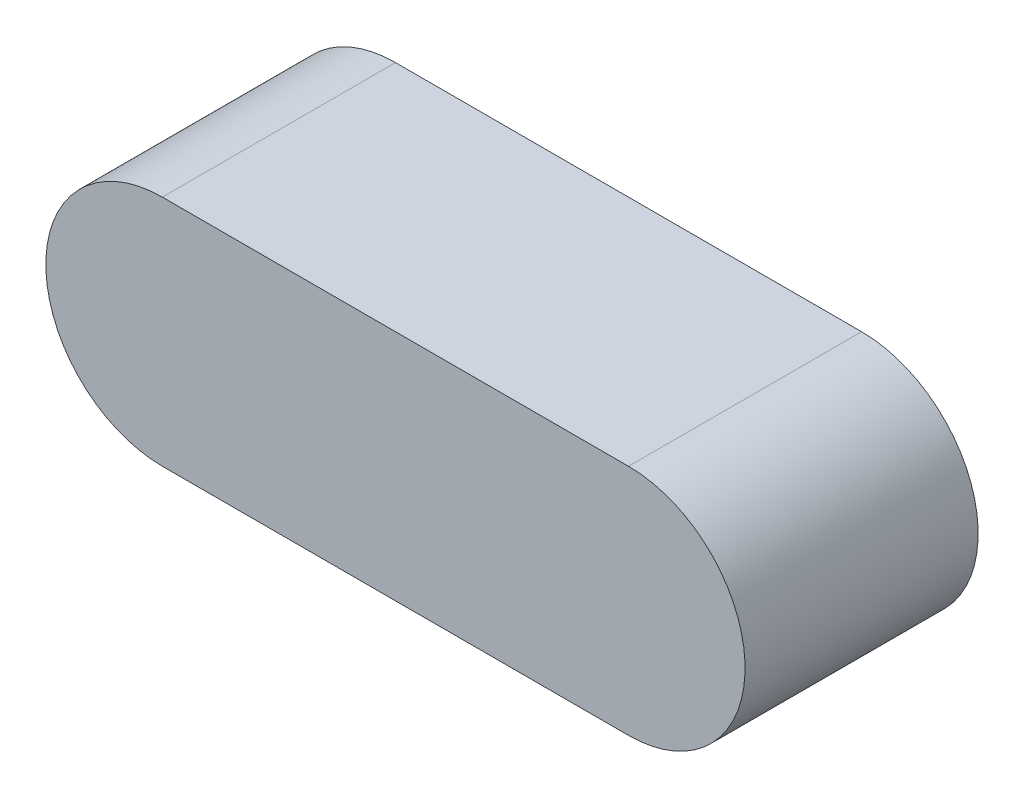
SolidWorks part; units mm, degrees
extrude "Base-Extrude" add sketch "Sketch1" along normal blind 3
sketch "Sketch1" plane through (0, 0, 0) normal (0, 0, 1) x (1, 0, 0)
  line L0 (-3, 1.5) -> (3, 1.5)
  line L1 (-3, -1.5) -> (3, -1.5)
  line L2 (-4.5, 0) -> (-4.5, 3.7182) construction
  line L3 (4.5, 0) -> (4.5, 3.2393) construction
  arc A0 (-3, 1.5) -> (-3, -1.5) centre (-3, 0) ccw
  arc A1 (3, -1.5) -> (3, 1.5) centre (3, 0) ccw
  dimension "D2" = 1.5
  dimension "D3" = 1.5
  dimension "D1" = 9
  dimension "D4" = 3
ref_plane "Front" through (0, 0, 0) normal (0, 0, 1) x (1, 0, 0)
ref_plane "Top" through (0, 0, 0) normal (0, 1, 0) x (1, 0, 0)
ref_plane "Right" through (0, 0, 0) normal (1, 0, 0) x (0, 0, -1)
